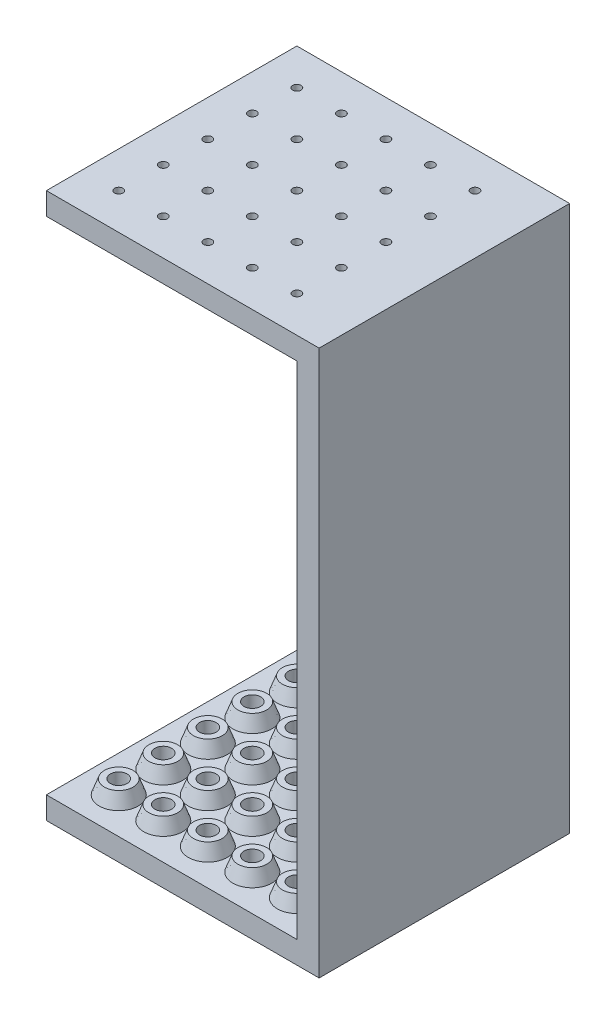
SolidWorks part; units mm, degrees
ref_plane "Front Plane" through (0, 0, 0) normal (0, 0, 1) x (1, 0, 0)
ref_plane "Top Plane" through (0, 0, 0) normal (0, 1, 0) x (1, 0, 0)
ref_plane "Right Plane" through (0, 0, 0) normal (1, 0, 0) x (0, 0, -1)
sketch "Sketch1" plane through (0, 0, 0) normal (0, 1, 0) x (1, 0, 0)
  line L1 (12.25, -11.25) -> (-12.25, -11.25)
  line L2 (12.25, -11.25) -> (12.25, 11.25)
  line L3 (12.25, 11.25) -> (-12.25, 11.25)
  line L4 (-12.25, -11.25) -> (-12.25, 11.25)
  line L5 (12.25, -11.25) -> (-12.25, 11.25) construction
  line L6 (12.25, 11.25) -> (-12.25, -11.25) construction
  point P0 (0, 0)
  dimension "D1" = 24.5
  dimension "D2" = 22.5
extrude "Boss-Extrude1" add sketch "Sketch1" along normal blind 2
sketch "Sketch2" plane through (0, 2, 0) normal (0, 1, 0) x (1, 0, 0)
  line L0 (-12.25, 11.25) -> (12.25, -11.25) construction
  line L1 (12.25, 11.25) -> (-12.25, -11.25) construction
  line L3 (12.25, 11.25) -> (-12.25, 11.25) construction
  line L5 (12.25, -11.25) -> (10.25, -11.25)
  line L7 (10.25, -11.25) -> (10.25, 11.25)
  line L8 (10.25, 11.25) -> (12.25, 11.25)
  line L9 (-12.25, -11.25) -> (12.25, -11.25) construction
  line L12 (12.25, 11.25) -> (12.25, -11.25)
  dimension "D2" = 2
extrude "Boss-Extrude2" add sketch "Sketch2" along normal blind 45
sketch "Sketch3" plane through (0, 0, 0) normal (0, -1, 0) x (1, 0, 0)
  line L0 (-9, 8) -> (-9, 11.25) construction
  line L1 (12.25, 11.25) -> (-12.25, -11.25) construction
  line L2 (-12.25, -11.25) -> (-12.25, 11.25) construction
  line L7 (-12.25, 11.25) -> (12.25, 11.25) construction
  circle A0 centre (-9, 8) radius 0.375
  dimension "D1" = 0.75
  dimension "D3" = 3.25
  dimension "D4" = 3.25
sketch "Sketch4" plane through (0, 47, 0) normal (0, 1, 0) x (1, 0, 0)
  line L1 (-12.25, 11.25) -> (12.25, 11.25)
  line L2 (-12.25, 11.25) -> (-12.25, -11.25)
  line L3 (-12.25, -11.25) -> (12.25, -11.25)
  line L4 (12.25, 11.25) -> (12.25, -11.25)
  line L5 (-12.25, 11.25) -> (12.25, -11.25) construction
  line L6 (-12.25, -11.25) -> (12.25, 11.25) construction
  point P0 (0, 0)
  dimension "D1" = 24.5
  dimension "D2" = 22.5
extrude "Boss-Extrude3" add sketch "Sketch4" along normal blind 2
extrude "Cut-Extrude1" cut sketch "Sketch3" against normal through all
sketch "Sketch5" plane through (0, 2, 0) normal (0, 1, 0) x (1, 0, 0)
  circle A0 centre (-9, -8) radius 1.75
  dimension "D1" = 3.5
extrude "Boss-Extrude4" add sketch "Sketch5" along normal blind 1.25 draft 20
sketch "Sketch6" plane through (0, 3.25, 0) normal (0, 1, 0) x (1, 0, 0)
  circle A0 centre (-9, -8) radius 0.75
  dimension "D1" = 1.5
extrude "Cut-Extrude2" cut sketch "Sketch6" against normal up to surface (1.25 mm away) up to face at (-1, 2, -2.8125)
pattern_linear "LPattern1" count 5 spacing 4 along (0, 0, -1) count 5 spacing 4 along (1, 0, 0) of "Cut-Extrude1", "Boss-Extrude4", "Cut-Extrude2"
equation "\"D1@Sketch1\"=\"D2@Sketch1\"+2"
equation "\"D4@Sketch3\"=\"D3@Sketch3\""
equation "\"D1@Sketch4\"=\"D2@Sketch4\"+2"
